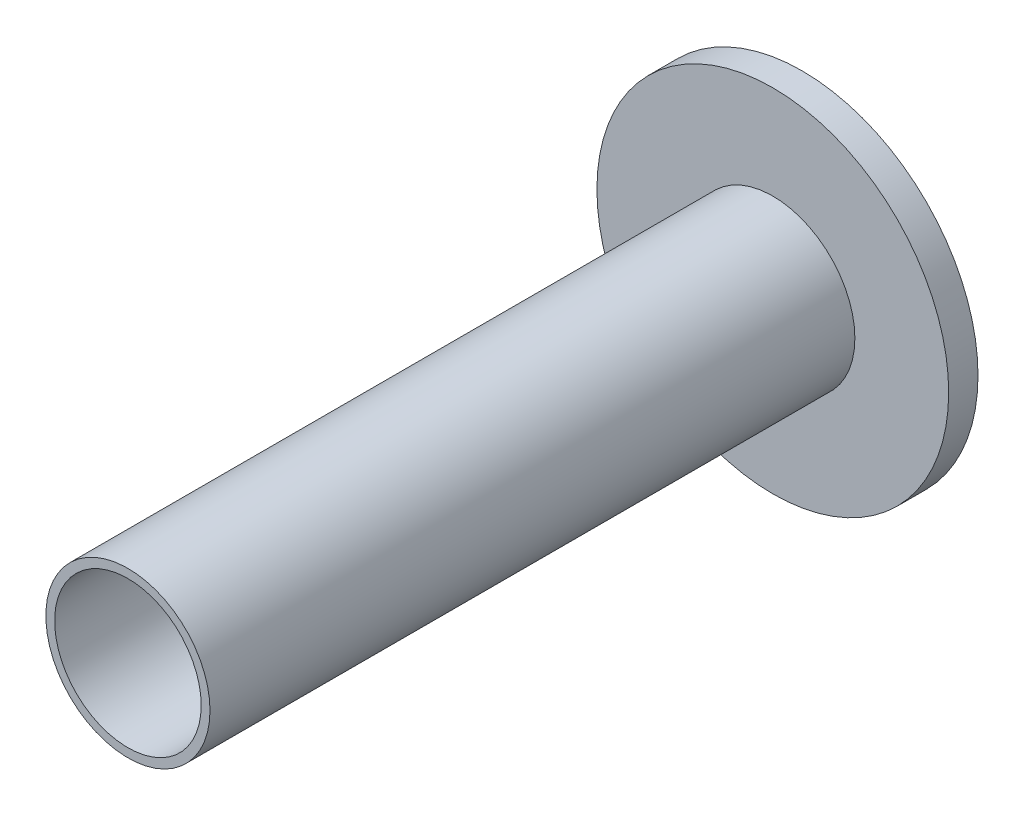
SolidWorks part; units mm, degrees
ref_plane "前视基准面" through (0, 0, 0) normal (0, 0, 1) x (1, 0, 0)
ref_plane "上视基准面" through (0, 0, 0) normal (0, 1, 0) x (1, 0, 0)
ref_plane "右视基准面" through (0, 0, 0) normal (1, 0, 0) x (0, 0, -1)
sketch "草图1" plane through (0, 0, 0) normal (0, 0, 1) x (1, 0, 0)
  circle A0 centre (0, 0) radius 6
extrude "凸台-拉伸1" add sketch "草图1" along normal blind 1
sketch "草图2" plane through (0, 0, 1) normal (0, 0, 1) x (1, 0, 0)
  circle A0 centre (0, 0) radius 2.8
  circle A1 centre (0, 0) radius 2.5
extrude "凸台-拉伸2" add sketch "草图2" along normal blind 22
